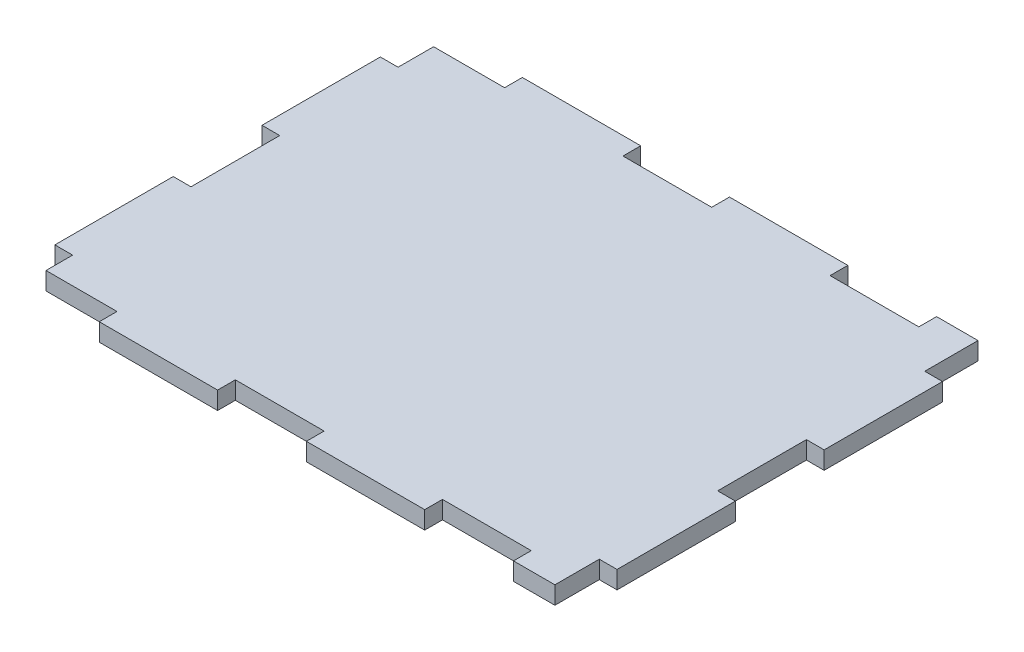
SolidWorks part; units mm, degrees
ref_plane "Front Plane" through (0, 0, 0) normal (0, 0, 1) x (1, 0, 0)
ref_plane "Top Plane" through (0, 0, 0) normal (0, 1, 0) x (1, 0, 0)
ref_plane "Right Plane" through (0, 0, 0) normal (1, 0, 0) x (0, 0, -1)
sketch "Sketch1" plane through (0, 0, 0) normal (0, 1, 0) x (1, 0, 0)
  line L0 (12, 65.5) -> (0, 65.5)
  line L1 (82, 0) -> (67, 0)
  line L2 (89, 0) -> (89, 4.5)
  line L3 (82, 65.5) -> (67, 65.5)
  line L4 (0, 0) -> (0, 4.5)
  line L5 (47, 65.5) -> (32, 65.5)
  line L6 (12, 65.5) -> (12, 68.5)
  line L7 (12, 68.5) -> (32, 68.5)
  line L8 (32, 65.5) -> (32, 68.5)
  line L11 (89, 59.5) -> (89, 65.5)
  line L12 (47, 65.5) -> (47, 68.5)
  line L13 (47, 68.5) -> (67, 68.5)
  line L14 (67, 65.5) -> (67, 68.5)
  line L15 (89, 65.5) -> (89, 68.5)
  line L16 (89, 68.5) -> (82, 68.5)
  line L17 (0, 59.5) -> (-3, 59.5)
  line L18 (82, 65.5) -> (82, 68.5)
  line L19 (0, 24.5) -> (-3, 24.5)
  line L20 (-3, 59.5) -> (-3, 39.5)
  line L21 (89, 0) -> (89, -3)
  line L22 (89, -3) -> (82, -3)
  line L23 (0, 39.5) -> (-3, 39.5)
  line L24 (0, 59.5) -> (0, 65.5)
  line L25 (0, 4.5) -> (-3, 4.5)
  line L26 (-3, 24.5) -> (-3, 4.5)
  line L27 (82, 0) -> (82, -3)
  line L29 (0, 39.5) -> (0, 24.5)
  line L30 (12, 0) -> (12, -3)
  line L31 (12, -3) -> (32, -3)
  line L32 (32, 0) -> (32, -3)
  line L35 (12, 0) -> (0, 0)
  line L36 (47, 0) -> (47, -3)
  line L37 (47, -3) -> (67, -3)
  line L38 (67, 0) -> (67, -3)
  line L41 (89, 4.5) -> (92, 4.5)
  line L42 (47, 0) -> (32, 0)
  line L43 (89, 39.5) -> (92, 39.5)
  line L44 (92, 4.5) -> (92, 24.5)
  line L47 (89, 59.5) -> (92, 59.5)
  line L48 (89, 39.5) -> (89, 24.5)
  line L49 (89, 24.5) -> (92, 24.5)
  line L50 (92, 59.5) -> (92, 39.5)
  point P24 (0, 0)
  dimension "D1" = 20
  dimension "D2" = 89
  dimension "D3" = 65.5
  dimension "D4" = 3
  dimension "D5" = 6
  dimension "D6" = 15
  dimension "D7" = 12
  dimension "D8" = 7
extrude "Boss-Extrude1" add sketch "Sketch1" along normal blind 3
